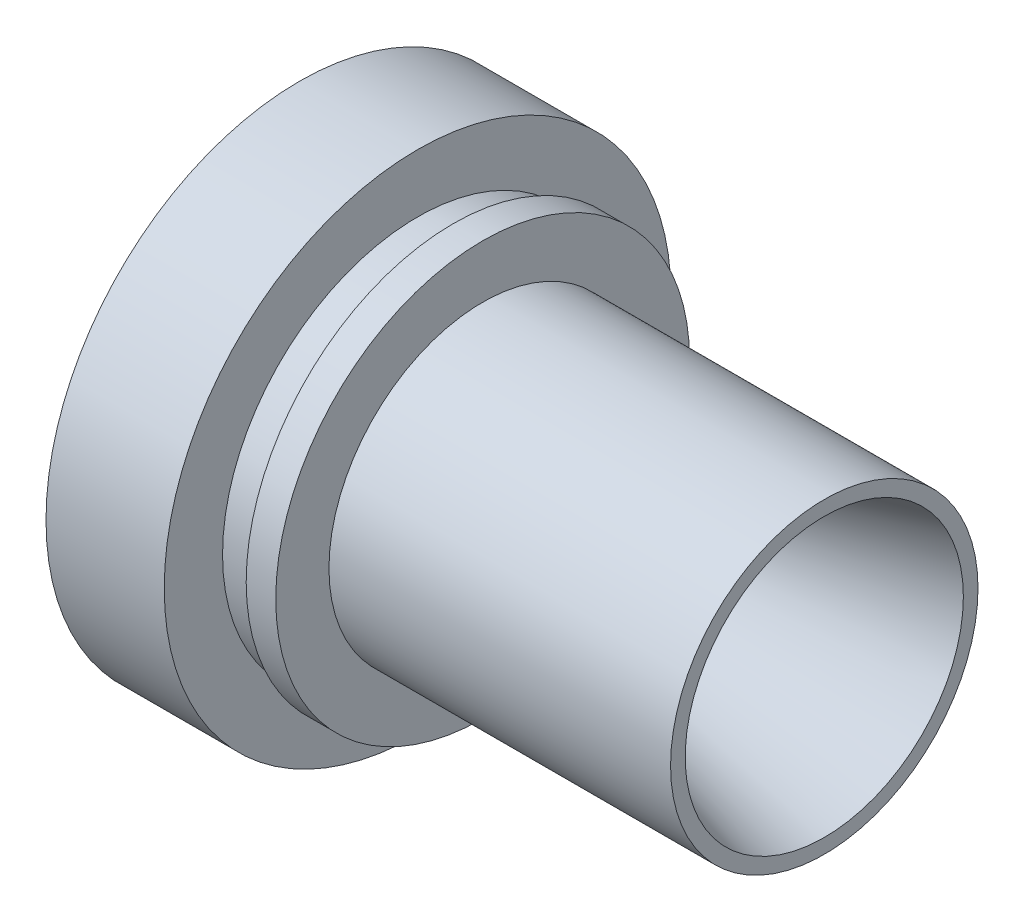
SolidWorks part; units mm, degrees
other "Markup1"
sketch "Sketch2" plane through (-20, 42.86, 42.86) normal (-0.0657, 0.2231, 0.9726) x (0.9978, 0.0263, 0.0614)
material "C (Graphite)"
ref_plane "Ebene vorne" through (0, 0, 0) normal (0, 0, 1) x (1, 0, 0)
ref_plane "Ebene oben" through (0, 0, 0) normal (0, 1, 0) x (1, 0, 0)
ref_plane "Ebene rechts" through (0, 0, 0) normal (1, 0, 0) x (0, 0, -1)
sketch "Sketch1" plane through (0, 0, 0) normal (0, 0, 1) x (1, 0, 0)
  line L0 (-20, 42.86) -> (7.8866, 14.9734)
  line L1 (22.3755, 11.0911) -> (68.7794, 23.525)
  line L3 (11, 26) -> (11, 35)
  line L4 (11, 35) -> (6, 35)
  line L5 (6, 35) -> (6, 33)
  line L6 (6, 33) -> (0, 33)
  line L7 (0, 33) -> (0, 42.86)
  line L9 (0, 42.86) -> (-20, 42.86)
  line L11 (0, 0) -> (-25.0058, 0) construction
  line L12 (68.7794, 23.525) -> (68.7794, 26)
  line L13 (68.7794, 26) -> (11, 26)
  arc A0 (7.8866, 14.9734) -> (22.3755, 11.0911) centre (18.4932, 25.58) ccw
  circle A1 centre (0, 33) radius 7.1701 construction
  circle A2 centre (11, 26) radius 9.9985 construction
  point P4 (0, 0)
  point P12 (0, 0)
  dimension "D1" = 45
  dimension "D3" = 15
  dimension "D4" = 25.58
  dimension "D9" = 33
  dimension "D8" = 20
  dimension "D2" = 15
  dimension "D5" = 23.525
  dimension "D6" = 26
  dimension "D7" = 42.86
  dimension "D10" = 2
  dimension "D12" = 5
  dimension "D13" = 6
revolve "Revolve1" add sketch "Sketch1" angle 360 about L11
